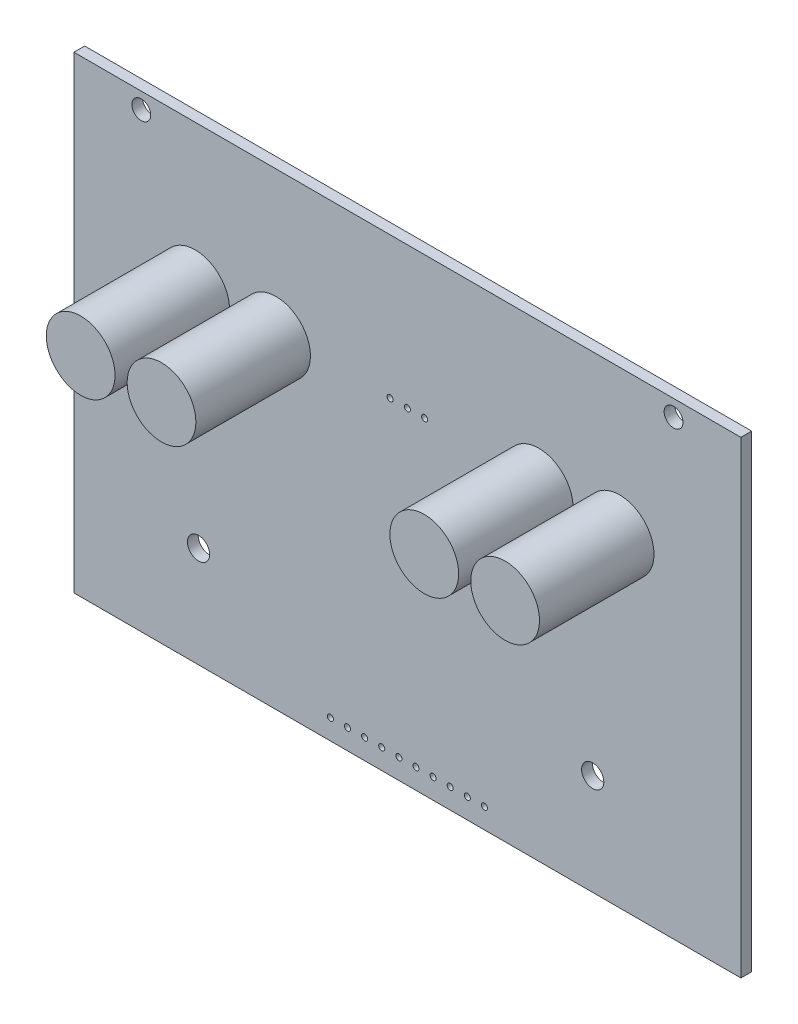
SolidWorks part; units mm, degrees
ref_plane "Front Plane" through (0, 0, 0) normal (0, 0, 1) x (1, 0, 0)
ref_plane "Top Plane" through (0, 0, 0) normal (0, 1, 0) x (1, 0, 0)
ref_plane "Right Plane" through (0, 0, 0) normal (1, 0, 0) x (0, 0, -1)
sketch "Sketch1" plane through (0, 0, 0) normal (0, 0, 1) x (1, 0, 0)
  line L1 (0, 0) -> (99, 0)
  line L2 (0, 0) -> (0, 69.5)
  line L3 (0, 69.5) -> (99, 69.5)
  line L4 (99, 0) -> (99, 69.5)
  dimension "D1" = 99
  dimension "D2" = 69.5
extrude "Boss-Extrude1" add sketch "Sketch1" along normal blind 1.6
sketch "Sketch2" plane through (0, 0, 1.6) normal (0, 0, 1) x (1, 0, 0)
  line L0 (0, 69.5) -> (0, 0) construction
  line L1 (99, 0) -> (99, 69.5) construction
  line L2 (99, 69.5) -> (0, 69.5) construction
  circle A0 centre (18, 48) radius 5.1
  circle A1 centre (30, 48) radius 5.1
  circle A2 centre (69, 48) radius 5.1
  circle A3 centre (81, 48) radius 5.1
  dimension "D1" = 10.2
  dimension "D2" = 18
  dimension "D3" = 30
  dimension "D4" = 18
  dimension "D5" = 30
  dimension "D6" = 21.5
extrude "Boss-Extrude2" add sketch "Sketch2" along normal blind 17
sketch "Sketch3" plane through (0, 0, 1.6) normal (0, 0, 1) x (1, 0, 0)
  line L0 (10, 67.1) -> (0, 67.1) construction
  line L1 (0, 69.5) -> (0, 0) construction
  line L2 (89, 67.1) -> (99, 67.1) construction
  line L3 (99, 0) -> (99, 69.5) construction
  line L4 (99, 69.5) -> (0, 69.5) construction
  line L5 (46.94, 48.5) -> (52.06, 48.5) construction
  line L6 (49.5, 69.5) -> (49.5, 0) construction
  line L7 (0, 0) -> (99, 0) construction
  line L8 (38.07, 3) -> (40.61, 3) construction
  line L9 (40.61, 3) -> (43.15, 3) construction
  line L10 (43.15, 3) -> (45.69, 3) construction
  line L11 (45.69, 3) -> (48.23, 3) construction
  line L12 (48.23, 3) -> (50.77, 3) construction
  line L13 (50.77, 3) -> (53.31, 3) construction
  line L14 (53.31, 3) -> (55.85, 3) construction
  line L15 (55.85, 3) -> (58.39, 3) construction
  line L16 (58.39, 3) -> (60.93, 3) construction
  circle A0 centre (10, 67.1) radius 1.4
  circle A1 centre (89, 67.1) radius 1.4
  circle A2 centre (18.5, 15) radius 1.65
  circle A3 centre (77, 15) radius 1.65
  circle A4 centre (49.5, 48.5) radius 0.45
  circle A5 centre (52.06, 48.5) radius 0.45
  circle A6 centre (46.94, 48.5) radius 0.45
  circle A7 centre (43.15, 3) radius 0.45
  circle A8 centre (45.69, 3) radius 0.45
  circle A9 centre (48.23, 3) radius 0.45
  circle A10 centre (50.77, 3) radius 0.45
  circle A11 centre (53.31, 3) radius 0.45
  circle A12 centre (55.85, 3) radius 0.45
  circle A13 centre (58.39, 3) radius 0.45
  circle A14 centre (60.93, 3) radius 0.45
  circle A15 centre (40.61, 3) radius 0.45
  circle A16 centre (38.07, 3) radius 0.45
  point P42 (49.5, 3)
  dimension "D1" = 3.3
  dimension "D2" = 2.8
  dimension "D5" = 0.9
  dimension "D3" = 10
  dimension "D4" = 2.4
  dimension "D6" = 5.12
  dimension "D7" = 21
  dimension "D8" = 2.54
  dimension "D9" = 66.5
  dimension "D10" = 54.5
  dimension "D11" = 22
  dimension "D12" = 80.5
extrude "Cut-Extrude1" cut sketch "Sketch3" against normal through all both and the other way through all
